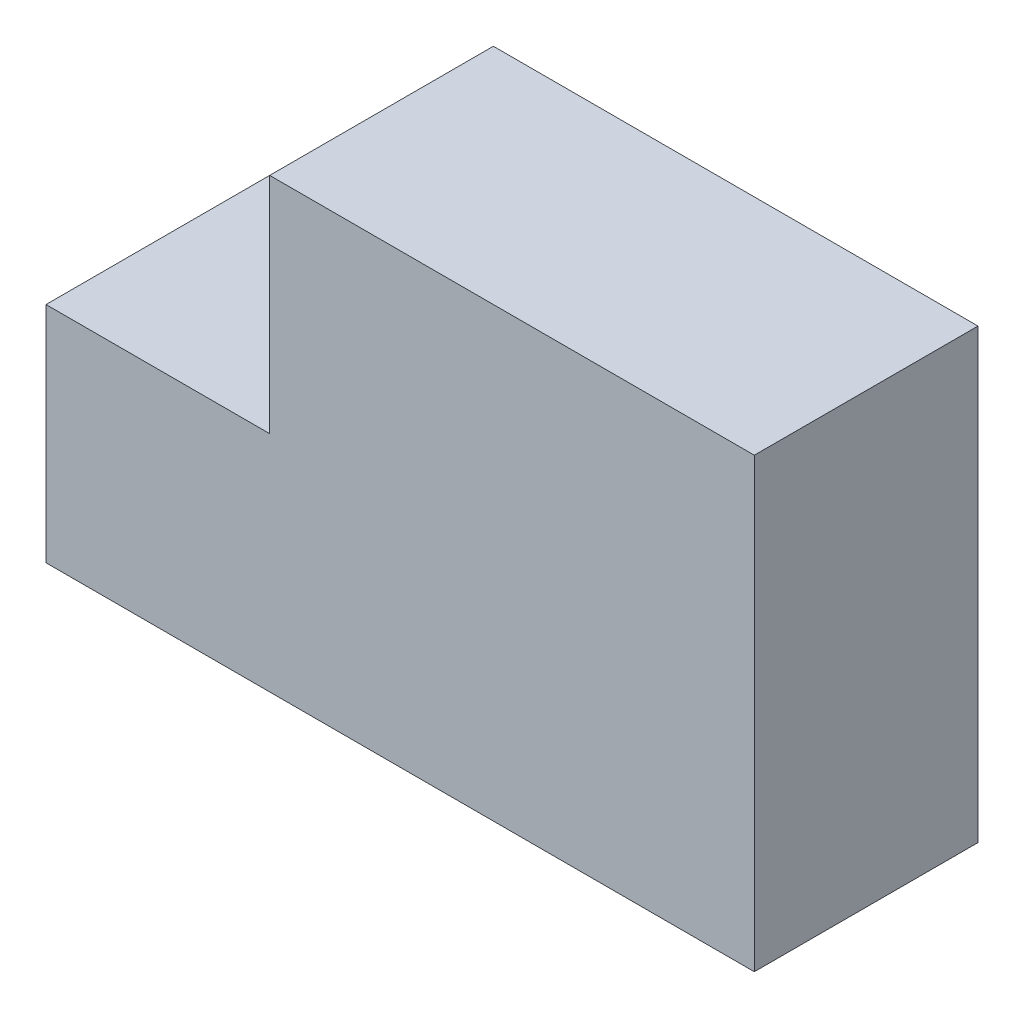
SolidWorks part; units mm, degrees
ref_plane "Plano frontal" through (0, 0, 0) normal (0, 0, 1) x (1, 0, 0)
ref_plane "Plano superior" through (0, 0, 0) normal (0, 1, 0) x (1, 0, 0)
ref_plane "Plano direito" through (0, 0, 0) normal (1, 0, 0) x (0, 0, -1)
sketch "Esboço1" plane through (0, 0, 0) normal (0, 0, 1) x (1, 0, 0)
  line L1 (0, 0) -> (19, 0)
  line L2 (0, 0) -> (0, 12)
  line L3 (0, 12) -> (19, 12)
  line L5 (0, 12) -> (6, 12)
  line L6 (0, 12) -> (0, 6)
  line L7 (0, 6) -> (6, 6)
  line L8 (6, 12) -> (6, 6)
  line L12 (19, 12) -> (19, 0)
  point P1 (19.3721, 0)
  dimension "D1" = 12
  dimension "D2" = 19
  dimension "D3" = 6
extrude "Ressalto-extrusão1" add sketch "Esboço1" along normal blind 6
